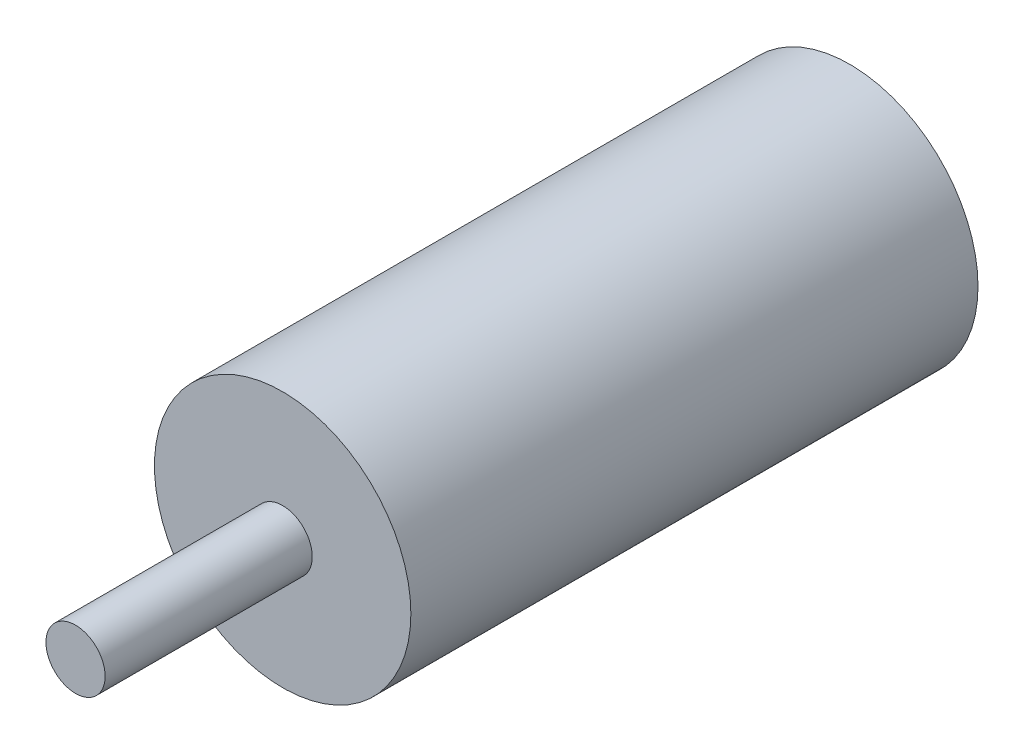
SolidWorks part; units mm, degrees
ref_plane "Front Plane" through (0, 0, 0) normal (0, 0, 1) x (1, 0, 0)
ref_plane "Top Plane" through (0, 0, 0) normal (0, 1, 0) x (1, 0, 0)
ref_plane "Right Plane" through (0, 0, 0) normal (1, 0, 0) x (0, 0, -1)
sketch "Sketch1" plane through (0, 0, 0) normal (0, 0, 1) x (1, 0, 0)
  circle A0 centre (0, 0) radius 26
  dimension "D1" = 52
extrude "Boss-Extrude1" add sketch "Sketch1" along normal blind 115
sketch "Sketch2" plane through (0, 0, 115) normal (0, 0, 1) x (1, 0, 0)
  circle A0 centre (0, 0) radius 6
  dimension "D1" = 12
extrude "Boss-Extrude2" add sketch "Sketch2" along normal blind 42
